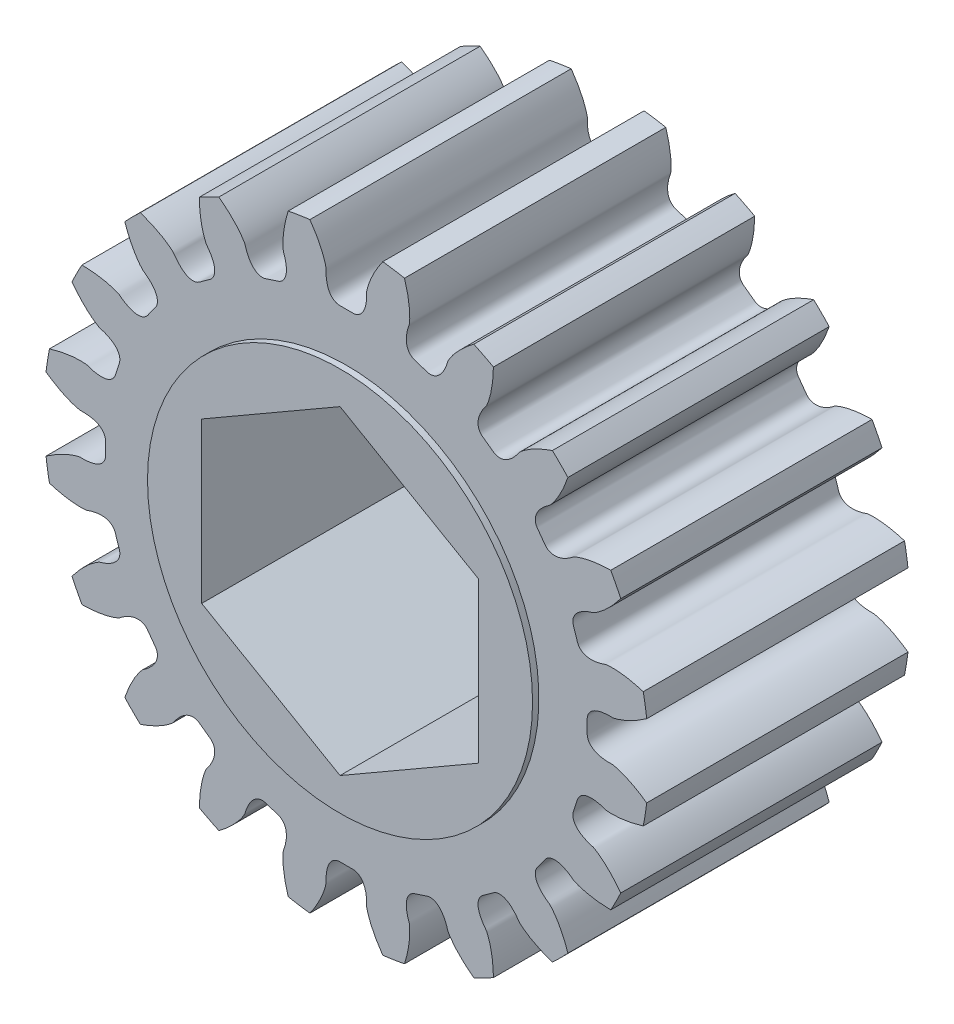
SolidWorks part; units mm, degrees
ref_plane "Front Plane" through (0, 0, 0) normal (0, 0, 1) x (1, 0, 0)
ref_plane "Top Plane" through (0, 0, 0) normal (0, 1, 0) x (1, 0, 0)
ref_plane "Right Plane" through (0, 0, 0) normal (1, 0, 0) x (0, 0, -1)
ref_plane "Plane1" through (0, 0, -6.0325) normal (0, 0, -1) x (-1, 0, 0)
sketch "Sketch1" plane through (0, 0, -6.0325) normal (0, 0, -1) x (-1, 0, 0)
  arc A0 (-9.5127, 10.2308) -> (-10.2308, 9.5127) centre (0, 0) ccw
  arc A1 (-12.2086, 6.7905) -> (-12.6697, 5.8856) centre (0, 0) ccw
  arc A2 (-13.7094, 2.6855) -> (-13.8683, 1.6824) centre (0, 0) ccw
  arc A3 (-13.8683, -1.6824) -> (-13.7094, -2.6855) centre (0, 0) ccw
  arc A4 (-12.6697, -5.8856) -> (-12.2086, -6.7905) centre (0, 0) ccw
  arc A5 (-10.2308, -9.5127) -> (-9.5127, -10.2308) centre (0, 0) ccw
  arc A6 (-6.7905, -12.2086) -> (-5.8856, -12.6697) centre (0, 0) ccw
  arc A7 (-2.6855, -13.7094) -> (-1.6824, -13.8683) centre (0, 0) ccw
  arc A8 (1.6824, -13.8683) -> (2.6855, -13.7094) centre (0, 0) ccw
  arc A9 (5.8856, -12.6697) -> (6.7905, -12.2086) centre (0, 0) ccw
  arc A10 (9.5127, -10.2308) -> (10.2308, -9.5127) centre (0, 0) ccw
  arc A11 (12.2086, -6.7905) -> (12.6697, -5.8856) centre (0, 0) ccw
  arc A12 (13.7094, -2.6855) -> (13.8683, -1.6824) centre (0, 0) ccw
  arc A13 (13.8683, 1.6824) -> (13.7094, 2.6855) centre (0, 0) ccw
  arc A14 (12.6697, 5.8856) -> (12.2086, 6.7905) centre (0, 0) ccw
  arc A15 (10.2308, 9.5127) -> (9.5127, 10.2308) centre (0, 0) ccw
  arc A16 (6.7905, 12.2086) -> (5.8856, 12.6697) centre (0, 0) ccw
  arc A17 (2.6855, 13.7094) -> (1.6824, 13.8683) centre (0, 0) ccw
  arc A18 (-1.6824, 13.8683) -> (-2.6855, 13.7094) centre (0, 0) ccw
  arc A19 (-5.8856, 12.6697) -> (-6.7905, 12.2086) centre (0, 0) ccw
  spline S0 degree 3 number of poles 113 (-12.2086, 6.7905) -> (-10.2308, 9.5127)
  spline S1 degree 3 number of poles 113 (-13.7094, 2.6855) -> (-12.6697, 5.8856)
  spline S2 degree 3 number of poles 113 (-13.8683, -1.6824) -> (-13.8683, 1.6824)
  spline S3 degree 3 number of poles 113 (-12.6697, -5.8856) -> (-13.7094, -2.6855)
  spline S4 degree 3 number of poles 113 (-10.2308, -9.5127) -> (-12.2086, -6.7905)
  spline S5 degree 3 number of poles 113 (-6.7905, -12.2086) -> (-9.5127, -10.2308)
  spline S6 degree 3 number of poles 113 (-2.6855, -13.7094) -> (-5.8856, -12.6697)
  spline S7 degree 3 number of poles 113 (1.6824, -13.8683) -> (-1.6824, -13.8683)
  spline S8 degree 3 number of poles 113 (5.8856, -12.6697) -> (2.6855, -13.7094)
  spline S9 degree 3 number of poles 113 (9.5127, -10.2308) -> (6.7905, -12.2086)
  spline S10 degree 3 number of poles 113 (12.2086, -6.7905) -> (10.2308, -9.5127)
  spline S11 degree 3 number of poles 113 (13.7094, -2.6855) -> (12.6697, -5.8856)
  spline S12 degree 3 number of poles 113 (13.8683, 1.6824) -> (13.8683, -1.6824)
  spline S13 degree 3 number of poles 113 (12.6697, 5.8856) -> (13.7094, 2.6855)
  spline S14 degree 3 number of poles 113 (10.2308, 9.5127) -> (12.2086, 6.7905)
  spline S15 degree 3 number of poles 113 (6.7905, 12.2086) -> (9.5127, 10.2308)
  spline S16 degree 3 number of poles 113 (2.6855, 13.7094) -> (5.8856, 12.6697)
  spline S17 degree 3 number of poles 113 (-1.6824, 13.8683) -> (1.6824, 13.8683)
  spline S18 degree 3 number of poles 113 (-5.8856, 12.6697) -> (-2.6855, 13.7094)
  spline S19 degree 3 number of poles 113 (-9.5127, 10.2308) -> (-6.7905, 12.2086)
extrude "Boss-Extrude1" add sketch "Sketch1" against normal blind 12.065
sketch "Sketch2" plane through (0, 0, -6.0325) normal (0, 0, -1) x (-1, 0, 0)
  circle A0 centre (0, 0) radius 8.89
extrude "Boss-Extrude2" add sketch "Sketch2" along normal blind 0.2921
sketch "Sketch3" plane through (0, 0, 6.0325) normal (0, 0, 1) x (1, 0, 0)
  circle A0 centre (0, 0) radius 8.89
extrude "Boss-Extrude3" add sketch "Sketch3" along normal blind 0.2921
sketch "Sketch4" plane through (0, 0, 6.3246) normal (0, 0, 1) x (1, 0, 0)
  line L0 (6.3881, -3.6882) -> (6.3881, 3.6882)
  line L1 (6.3881, 3.6882) -> (0, 7.3763)
  line L2 (0, 7.3763) -> (-6.3881, 3.6882)
  line L3 (-6.3881, 3.6882) -> (-6.3881, -3.6882)
  line L4 (-6.3881, -3.6882) -> (0, -7.3763)
  line L5 (0, -7.3763) -> (6.3881, -3.6882)
extrude "Cut-Extrude1" cut sketch "Sketch4" against normal through all
